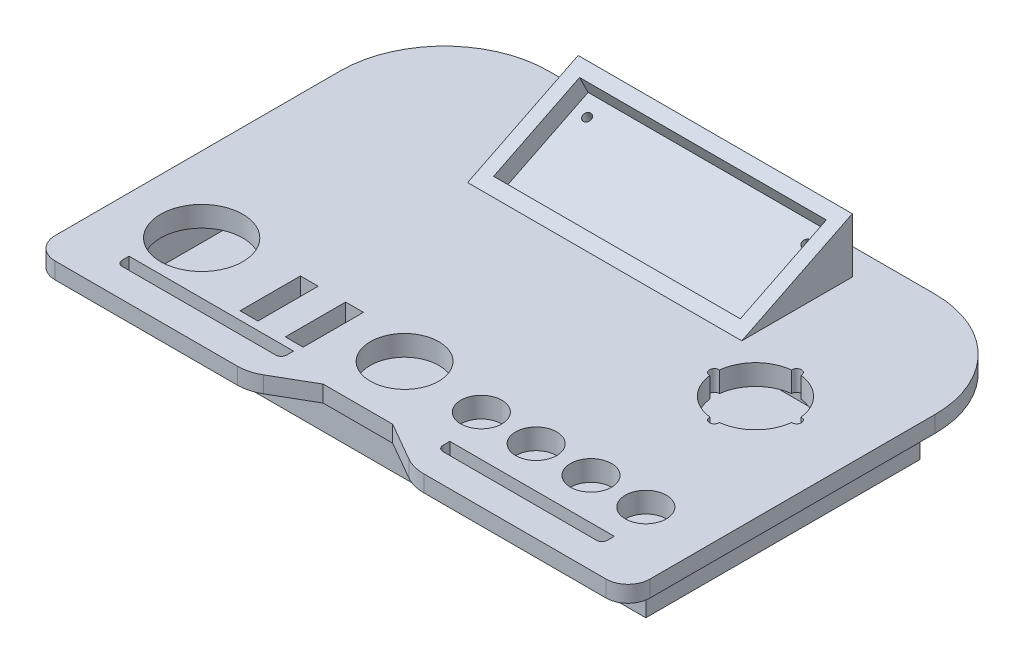
SolidWorks part; units mm, degrees
ref_plane "Ön Düzlem" through (0, 0, 0) normal (0, 0, 1) x (1, 0, 0)
ref_plane "Üst Düzlem" through (0, 0, 0) normal (0, 1, 0) x (1, 0, 0)
ref_plane "Sağ Düzlem" through (0, 0, 0) normal (1, 0, 0) x (0, 0, -1)
sketch "Çizim2" plane through (0, 0, 0) normal (0, 1, 0) x (1, 0, 0)
  line L1 (0, 0) -> (-200, 0)
  line L2 (0, 0) -> (0, 100)
  line L3 (0, 100) -> (-200, 100)
  line L4 (-200, 0) -> (-200, 100)
  dimension "D1" = 200
  dimension "D2" = 100
extrude "Yükseklik-Ekstrüzyon1" add sketch "Çizim2" along normal blind 20
sketch "Çizim3" plane through (0, 20, 0) normal (0, 1, 0) x (1, 0, 0)
  line L0 (0, 0) -> (0, 100) construction
  line L1 (0, 100) -> (-200, 100) construction
  line L2 (-200, 100) -> (-200, 0) construction
  line L3 (-200, 0) -> (0, 0) construction
  line L5 (-151, 25) -> (-144.5, 25)
  line L6 (-151, 25) -> (-151, 3)
  line L7 (-151, 3) -> (-144.5, 3)
  line L8 (-144.5, 25) -> (-144.5, 3)
  line L9 (-134.5, 25) -> (-128, 25)
  line L10 (-134.5, 25) -> (-134.5, 3)
  line L11 (-134.5, 3) -> (-128, 3)
  line L12 (-128, 25) -> (-128, 3)
  arc A0 (-44.8979, 68.253) -> (-31.747, 55.1021) centre (-30, 70) ccw
  arc A2 (-31.747, 55.1021) -> (-28.253, 55.1021) centre (-30, 55) ccw
  arc A3 (-44.8979, 71.747) -> (-44.8979, 68.253) centre (-45, 70) ccw
  arc A4 (-28.253, 84.8979) -> (-31.747, 84.8979) centre (-30, 85) ccw
  arc A5 (-15.1021, 68.253) -> (-15.1021, 71.747) centre (-15, 70) ccw
  arc A6 (-31.747, 84.8979) -> (-44.8979, 71.747) centre (-30, 70) ccw
  arc A7 (-15.1021, 71.747) -> (-28.253, 84.8979) centre (-30, 70) ccw
  arc A8 (-28.253, 55.1021) -> (-15.1021, 68.253) centre (-30, 70) ccw
  circle A9 centre (-15, 15) radius 7.5
  circle A10 centre (-35, 15) radius 7.5
  circle A11 centre (-55, 15) radius 7.5
  circle A12 centre (-75, 15) radius 7.5
  circle A13 centre (-105, 17) radius 12.5
  circle A14 centre (-181, 19) radius 15
  point P17 (-30, 70)
  point P31 (0, 0)
  point P43 (-105, 20.9549)
  point P44 (0, 0)
  point P45 (-105, 12.3143)
  point P46 (-105, 17.351)
  point P47 (-180.6098, 19.7192)
  dimension "D1" = 30
  dimension "D4" = 3.5
  dimension "D6" = 30
  dimension "D7" = 15
  dimension "D10" = 15
  dimension "D14" = 25
  dimension "D16" = 30
  dimension "D2" = 30
  dimension "D3" = 30
  dimension "D8" = 15
  dimension "D9" = 15
  dimension "D11" = 20
  dimension "D12" = 20
  dimension "D13" = 20
  dimension "D15" = 95
  dimension "D17" = 25
  dimension "D18" = 25
  dimension "D19" = 10
  dimension "D20" = 6.5
  dimension "D21" = 6.5
  dimension "D22" = 3
  dimension "D23" = 30
  dimension "D24" = 46.5
  dimension "D25" = 17
  dimension "D26" = 19
  dimension "D27" = 19
  dimension "D5" = 4
extrude "Kes-Ekstrüzyon11" cut sketch "Çizim3" against normal blind 12
sketch "Çizim4" plane through (0, 20, 0) normal (0, 1, 0) x (1, 0, 0)
  text T0 "motor hızı"
  text T1 "off"
  text T2 "on"
  text T3 "acil durum"
  text T4 "1"
  text T5 "2"
  text T6 "3"
  text T7 "4"
  text T8 "joystick"
  point P9 (0, 0)
sketch "Çizim7" plane through (0, 20, 0) normal (0, 1, 0) x (1, 0, 0)
  line L0 (-100, 0) -> (-100, -37.309) construction
  line L1 (-200, 0) -> (0, 0) construction
  line L2 (-87.3205, -5) -> (-112.6795, -5)
  line L3 (-112.6795, -5) -> (-126.5192, -12.9904)
  line L4 (-134.0192, -15) -> (-200.5, -15)
  line L5 (-208.5, -7) -> (-208.5, 97)
  line L6 (-170.5, 135) -> (-29.5, 135)
  line L7 (-100, 0) -> (-100, 151.0688) construction
  line L8 (-128.5, 0) -> (-128.5, -2.5)
  line L9 (-130.5, -4.5) -> (-186.5, -4.5)
  line L10 (-188.5, -2.5) -> (-188.5, 0)
  line L11 (0, 100) -> (-200, 100) construction
  line L12 (-11.5, -2.5) -> (-11.5, 0)
  line L13 (-71.5, 0) -> (-71.5, -2.5)
  line L14 (-69.5, -4.5) -> (-13.5, -4.5)
  line L15 (-87.3205, -5) -> (-73.4808, -12.9904)
  line L16 (-65.9808, -15) -> (0.5, -15)
  line L17 (8.5, -7) -> (8.5, 97)
  arc A0 (-126.5192, -12.9904) -> (-134.0192, -15) centre (-134.0192, 0) cw
  arc A1 (-186.5, -4.5) -> (-188.5, -2.5) centre (-186.5, -2.5) cw
  arc A2 (-128.5, -2.5) -> (-130.5, -4.5) centre (-130.5, -2.5) cw
  arc A3 (-208.5, -7) -> (-200.5, -15) centre (-200.5, -7) ccw
  arc A4 (-170.5, 135) -> (-208.5, 97) centre (-170.5, 97) ccw
  arc A5 (-13.5, -4.5) -> (-11.5, -2.5) centre (-13.5, -2.5) ccw
  arc A6 (-71.5, -2.5) -> (-69.5, -4.5) centre (-69.5, -2.5) ccw
  arc A7 (-73.4808, -12.9904) -> (-65.9808, -15) centre (-65.9808, 0) ccw
  arc A8 (8.5, -7) -> (0.5, -15) centre (0.5, -7) cw
  arc A9 (-29.5, 135) -> (8.5, 97) centre (-29.5, 97) cw
  point P17 (-130, -15)
  point P20 (-188.5, -4.5)
  point P23 (-128.5, -4.5)
  point P39 (-100, -5)
  point P48 (-100, 135)
  line M33 (0, 0) -> (0, 100)
  line M34 (0, 100) -> (-200, 100)
  line M35 (-200, 100) -> (-200, 0)
  line M36 (-200, 0) -> (0, 0)
  dimension "D9" = 15
  dimension "D10" = 2
  dimension "D11" = 8
  dimension "D13" = 38
  dimension "D1" = 5
  dimension "D2" = 150
  dimension "D3" = 15
  dimension "D4" = 30
  dimension "D5" = 20
  dimension "D6" = 60
  dimension "D7" = 4.5
  dimension "D8" = 1.5
  dimension "D12" = 35
extrude "Yükseklik-Ekstrüzyon2" add sketch "Çizim7" against normal blind 6 contours A9 L6 A4 L5 A3 L4 A0 L3 L2 L15 A7 L16 A8 L17 A6 L13 L8 A2 L9 A1 L10 L12 A5 L14 M36 M35 M34 M33
ref_plane "Düzlem1" through (-100, 0, 0) normal (1, 0, 0) x (0, 0, -1)
sketch "Çizim8" plane through (-100, 0, 0) normal (1, 0, 0) x (0, 0, -1)
  line L0 (-7, 20) -> (97, 20) construction
  line L1 (85, 20) -> (125.3113, 40)
  line L2 (125.3113, 40) -> (125.3113, 20)
  line L3 (135, 20) -> (97, 20) construction
  line L4 (125.3113, 20) -> (85, 20)
  line L6 (0, 20) -> (0, 54.0546) construction
  point P11 (109.8193, 35)
  dimension "D1" = 45
  dimension "D2" = 20
  dimension "D3" = 85
extrude "Yükseklik-Ekstrüzyon3" add sketch "Çizim8" along normal mid plane 100
sketch "Çizim9" plane through (0, -17.7922, -8.8274) normal (0, 0.8958, 0.4444) x (1, 0, 0)
  line L0 (-50, 130.0324) -> (-150, 130.0324) construction
  line L5 (-145, 125.0324) -> (-55, 125.0324)
  line L6 (-145, 125.0324) -> (-145, 90.0324)
  line L7 (-145, 90.0324) -> (-55, 90.0324)
  line L8 (-55, 125.0324) -> (-55, 90.0324)
  line L9 (-150, 130.0324) -> (-150, 85.0324) construction
  line L10 (-50, 85.0324) -> (-150, 85.0324) construction
  dimension "D1" = 5
  dimension "D2" = 5
  dimension "D3" = 90
  dimension "D4" = 5
extrude "Kes-Ekstrüzyon12" cut sketch "Çizim9" against normal blind 7
sketch "Çizim12" plane through (0, -24.0628, -11.9385) normal (0, 0.8958, 0.4444) x (1, 0, 0)
  line L0 (-145, 125.0324) -> (-145, 90.0324) construction
  line L1 (-55, 125.0324) -> (-145, 125.0324) construction
  circle A0 centre (-140, 119.0324) radius 1.5
  circle A1 centre (-60, 119.0324) radius 1.5
  dimension "D1" = 3
  dimension "D2" = 3
  dimension "D3" = 80
  dimension "D4" = 5
  dimension "D5" = 6
  dimension "D6" = 6
extrude "Kes-Ekstrüzyon14" cut sketch "Çizim12" against normal through all
ref_plane "Düzlem3" through (0, 0, -95) normal (0, 0, -1) x (-1, 0, 0)
sketch "Çizim15" plane through (0, 0, -95) normal (0, 0, -1) x (-1, 0, 0)
  line L0 (0, 14) -> (0, 0) construction
  line L1 (2, 12.5) -> (198, 12.5)
  line L2 (2, 12.5) -> (2, 1.5)
  line L3 (2, 1.5) -> (198, 1.5)
  line L4 (198, 12.5) -> (198, 1.5)
  line L5 (0, 0) -> (200, 0) construction
  line L6 (0, 14) -> (200, 14) construction
  line L7 (200, 14) -> (200, 0) construction
  dimension "D1" = 2
  dimension "D2" = 1.5
  dimension "D3" = 1.5
  dimension "D4" = 2
extrude "Kes-Ekstrüzyon15" cut sketch "Çizim15" against normal blind 92
sketch "Çizim16" plane through (0, 0, -100) normal (0, 0, -1) x (-1, 0, 0)
  line L0 (0, 0) -> (200, 0) construction
  line L1 (0, 14) -> (0, 0) construction
  line L2 (200, 14) -> (200, 0) construction
  circle A1 centre (65, 8) radius 1.5
  circle A2 centre (135, 8) radius 1.5
  dimension "D1" = 3
  dimension "D2" = 3
  dimension "D3" = 8
  dimension "D4" = 65
  dimension "D5" = 65
  dimension "D6" = 8
extrude "Kes-Ekstrüzyon16" cut sketch "Çizim16" against normal blind 10
